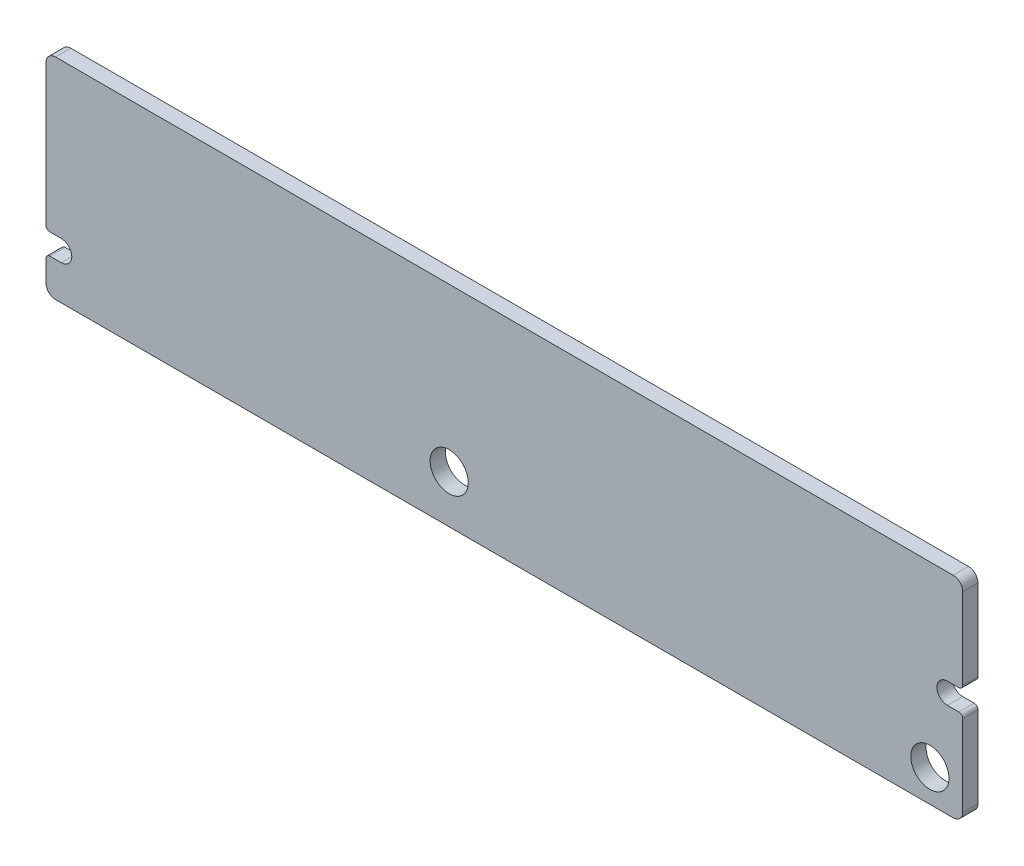
SolidWorks part; units mm, degrees
ref_plane "Front Plane" through (0, 0, 0) normal (0, 0, 1) x (1, 0, 0)
ref_plane "Top Plane" through (0, 0, 0) normal (0, 1, 0) x (1, 0, 0)
ref_plane "Right Plane" through (0, 0, 0) normal (1, 0, 0) x (0, 0, -1)
sketch "Sketch1" plane through (0, 0, -3.67) normal (0, 0, 1) x (1, 0, 0)
  line L20 (-47.1, 0.52) -> (-46.5, 0.52)
  line L21 (-46.5, -0.58) -> (-47.1, -0.58)
  line L22 (-47.3, -0.78) -> (-47.3, -1.9)
  line L23 (-46.8, -2.4) -> (0.2, -2.4)
  line L24 (0.7, -1.9) -> (0.7, 2.35)
  line L25 (0.5, 2.55) -> (-0.1, 2.55)
  line L26 (-0.1, 3.65) -> (0.5, 3.65)
  line L27 (0.7, 3.85) -> (0.7, 8.1)
  line L28 (0.2, 8.6) -> (-46.8, 8.6)
  line L29 (-47.3, 8.1) -> (-47.3, 0.72)
  arc A4 (-2.02, -0.72) -> (-0.02, -0.72) centre (-1.02, -0.72) ccw
  arc A5 (-0.02, -0.72) -> (-2.02, -0.72) centre (-1.02, -0.72) ccw
  arc A8 (-27.19, 0.1) -> (-25.19, 0.1) centre (-26.19, 0.1) ccw
  arc A9 (-25.19, 0.1) -> (-27.19, 0.1) centre (-26.19, 0.1) ccw
  arc A28 (-46.5, -0.58) -> (-46.5, 0.52) centre (-46.5, -0.03) ccw
  arc A29 (-47.1, -0.58) -> (-47.3, -0.78) centre (-47.1, -0.78) ccw
  arc A30 (-47.3, -1.9) -> (-46.8, -2.4) centre (-46.8, -1.9) ccw
  arc A31 (0.2, -2.4) -> (0.7, -1.9) centre (0.2, -1.9) ccw
  arc A32 (0.7, 2.35) -> (0.5, 2.55) centre (0.5, 2.35) ccw
  arc A33 (-0.1, 3.65) -> (-0.1, 2.55) centre (-0.1, 3.1) ccw
  arc A34 (0.5, 3.65) -> (0.7, 3.85) centre (0.5, 3.85) ccw
  arc A35 (0.7, 8.1) -> (0.2, 8.6) centre (0.2, 8.1) ccw
  arc A36 (-46.8, 8.6) -> (-47.3, 8.1) centre (-46.8, 8.1) ccw
  arc A37 (-47.3, 0.72) -> (-47.1, 0.52) centre (-47.1, 0.72) ccw
extrude "Boss-Extrude1" add sketch "Sketch1" against normal up to surface (0.8 mm away)
sketch "Sketch2" plane through (0, 0, -4.47) normal (0, 0, -1) x (-1, 0, 0)
  line L1 (19.8561, 4.0794) -> (22.6531, 4.0794)
  line L2 (19.8561, 4.0794) -> (19.8561, 1.0281)
  line L3 (19.8561, 1.0281) -> (22.6531, 1.0281)
  line L4 (22.6531, 4.0794) -> (22.6531, 1.0281)
  line L5 (26.34, 3.7615) -> (30.5568, 3.7615)
  line L6 (26.34, 3.7615) -> (26.34, 1.3671)
  line L7 (26.34, 1.3671) -> (30.5568, 1.3671)
  line L8 (30.5568, 3.7615) -> (30.5568, 1.3671)
extrude "Boss-Extrude2" add sketch "Sketch2" along normal blind 1.5 contours L2 L1 L4 L3 | L6 L5 L8 L7
